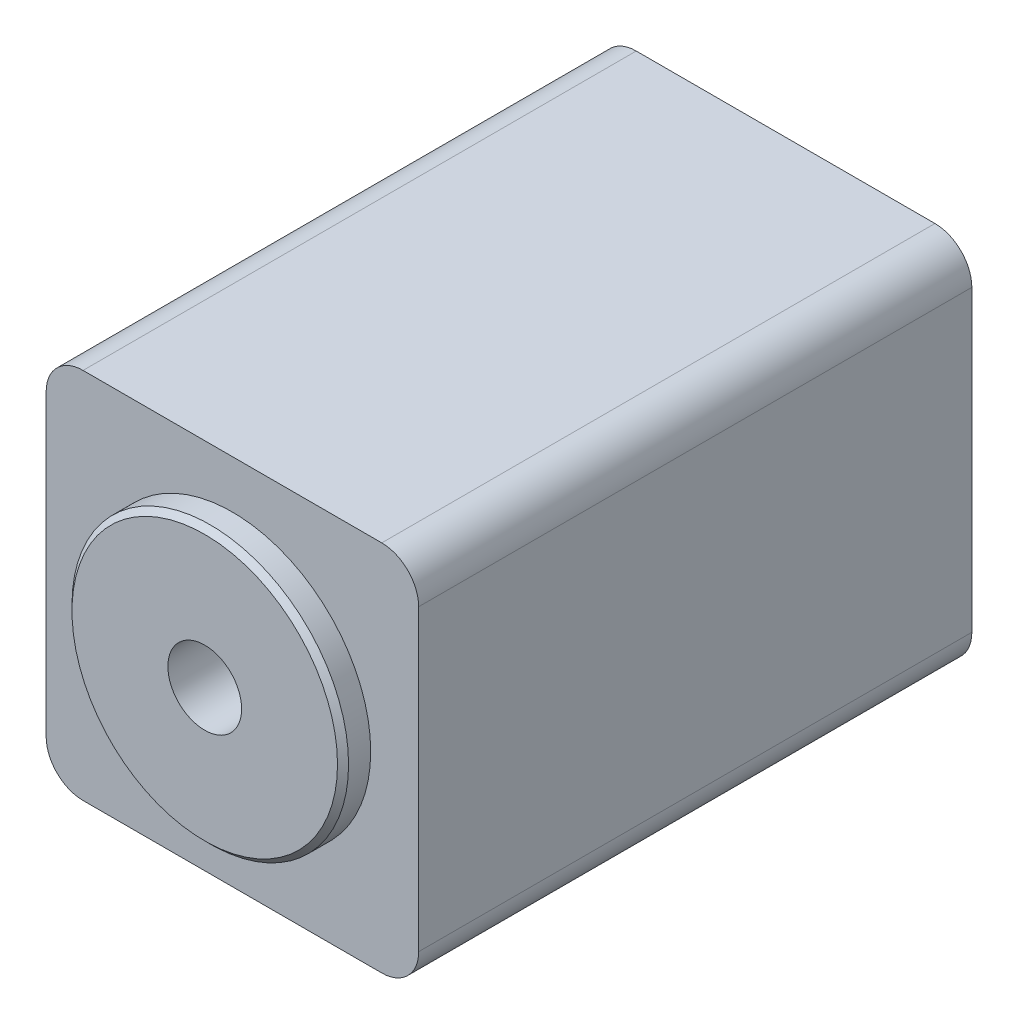
SolidWorks part; units mm, degrees
material "Laiton"
ref_plane "Plan de face" through (0, 0, 0) normal (0, 0, 1) x (1, 0, 0)
ref_plane "Plan de dessus" through (0, 0, 0) normal (0, 1, 0) x (1, 0, 0)
ref_plane "Plan de droite" through (0, 0, 0) normal (1, 0, 0) x (0, 0, -1)
sketch "Esquisse1" plane through (0, 0, 0) normal (0, 0, 1) x (1, 0, 0)
  circle A0 centre (0, 0) radius 7.5
  dimension "D1" = 15
extrude "Boss.-Extru.1" add sketch "Esquisse1" along normal blind 1.5
sketch "Esquisse2" plane through (0, 0, 0) normal (0, 0, -1) x (-1, 0, 0)
  line L1 (-10.1, 10.1) -> (10.1, 10.1)
  line L2 (-10.1, 10.1) -> (-10.1, -10.1)
  line L3 (-10.1, -10.1) -> (10.1, -10.1)
  line L4 (10.1, 10.1) -> (10.1, -10.1)
  line L5 (-10.1, 10.1) -> (10.1, -10.1) construction
  line L6 (-10.1, -10.1) -> (10.1, 10.1) construction
  point P0 (0, 0)
  dimension "D1" = 20.2
extrude "Boss.-Extru.2" add sketch "Esquisse2" along normal blind 30
sketch "Esquisse6" plane through (0, 0, 1.5) normal (0, 0, 1) x (1, 0, 0)
  circle A0 centre (0, 0) radius 2
  dimension "D1" = 4
extrude "Enlèv. mat.-Extru.1" cut sketch "Esquisse6" against normal blind 10
chamfer "Chanfrein1" distance 0.3 angle 45 1 edges at (7.5, 0, 1.5)
fillet "Congé1" radius 2 4 edges at (-10.1, -10.1, -15) (10.1, -10.1, -15) (-10.1, 10.1, -15) (10.1, 10.1, -15)
